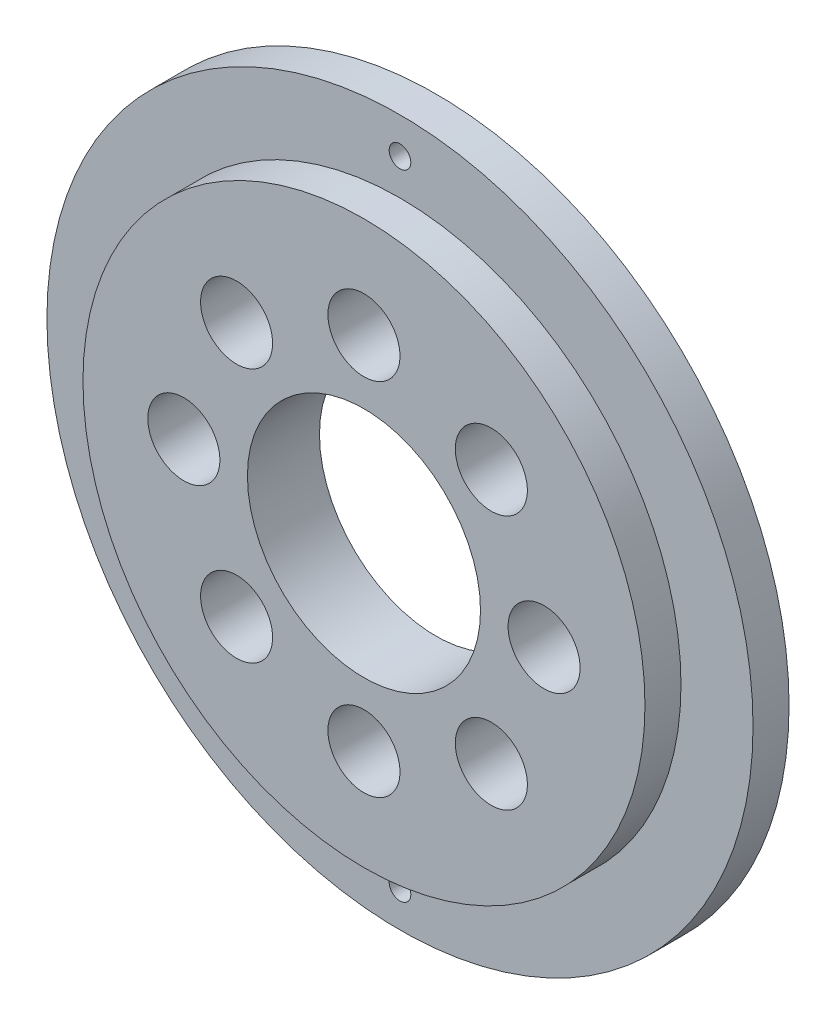
SolidWorks part; units mm, degrees
ref_plane "Plan de face" through (0, 0, 0) normal (0, 0, 1) x (1, 0, 0)
ref_plane "Plan de dessus" through (0, 0, 0) normal (0, 1, 0) x (1, 0, 0)
ref_plane "Plan de droite" through (0, 0, 0) normal (1, 0, 0) x (0, 0, -1)
sketch "Esquisse1" plane through (0, 0, 0) normal (0, 0, 1) x (1, 0, 0)
  circle A0 centre (0, 0) radius 39
  circle A1 centre (0, 0) radius 16.175
  dimension "D1" = 78
  dimension "D2" = 32.35
extrude "Boss.-Extru.1" add sketch "Esquisse1" along normal blind 5
sketch "Esquisse2" plane through (0, 0, 0) normal (0, 0, -1) x (-1, 0, 0)
  circle A0 centre (0, 0) radius 49
  circle A1 centre (0, 0) radius 39 construction
  dimension "D1" = 10
extrude "Boss.-Extru.2" add sketch "Esquisse2" along normal blind 5
sketch "Esquisse3" plane through (0, 0, -5) normal (0, 0, -1) x (-1, 0, 0)
  circle A0 centre (0, 0) radius 16.175
  circle A1 centre (0, 0) radius 16.175 construction
extrude "Enlèv. mat.-Extru.1" cut sketch "Esquisse3" against normal through all
sketch "Esquisse4" plane through (0, 0, -5) normal (0, 0, -1) x (-1, 0, 0)
  line L0 (0, -39) -> (0, -49) construction
  line L1 (0, 49) -> (0, 39) construction
  circle A0 centre (0, 0) radius 49 construction
  circle A1 centre (0, 44) radius 1.5
  circle A2 centre (0, -44) radius 1.5
  circle A3 centre (25, 0) radius 5
  circle A4 centre (0, 0) radius 39 construction
  circle A5 centre (0, 25) radius 5
  circle A6 centre (-25, 0) radius 5
  circle A7 centre (0, -25) radius 5
  circle A8 centre (-17.6777, -17.6777) radius 5
  circle A9 centre (17.6777, 17.6777) radius 5
  circle A10 centre (17.6777, -17.6777) radius 5
  circle A11 centre (-17.6777, 17.6777) radius 5
  dimension "D1" = 3
  dimension "D2" = 10
  dimension "D3" = 10
  dimension "D4" = 10
  dimension "D5" = 10
  dimension "D10" = 10
  dimension "D12" = 10
  dimension "D14" = 10
  dimension "D16" = 10
  dimension "D6" = 25
  dimension "D7" = 25
  dimension "D8" = 25
  dimension "D9" = 25
  dimension "D11" = 25
  dimension "D13" = 25
  dimension "D15" = 25
  dimension "D17" = 25
extrude "Enlèv. mat.-Extru.2" cut sketch "Esquisse4" against normal through all
